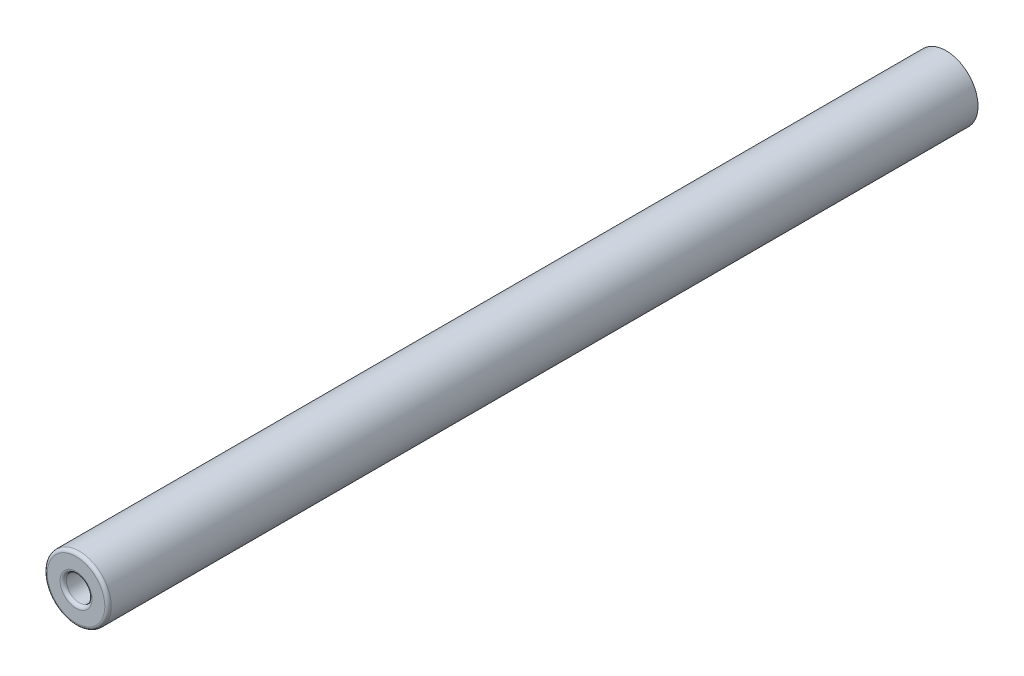
SolidWorks part; units mm, degrees
ref_plane "Front Plane" through (0, 0, 0) normal (0, 0, 1) x (1, 0, 0)
ref_plane "Top Plane" through (0, 0, 0) normal (0, 1, 0) x (1, 0, 0)
ref_plane "Right Plane" through (0, 0, 0) normal (1, 0, 0) x (0, 0, -1)
sketch "Sketch1" plane through (0, 0, 0) normal (0, 0, 1) x (1, 0, 0)
  circle A0 centre (0, 0) radius 5
  dimension "D1" = 10
extrude "Boss-Extrude1" add sketch "Sketch1" along normal blind 136
sketch "Sketch2" plane through (0, 0, 136) normal (0, 0, 1) x (1, 0, 0)
  circle A0 centre (0, 0) radius 2
  dimension "D1" = 4
extrude "Cut-Extrude1" cut sketch "Sketch2" against normal blind 20
fillet "Fillet1" radius 0.5 1 edges at (5, 0, 136)
fillet "Fillet2" radius 0.5 1 edges at (2, 0, 136)
